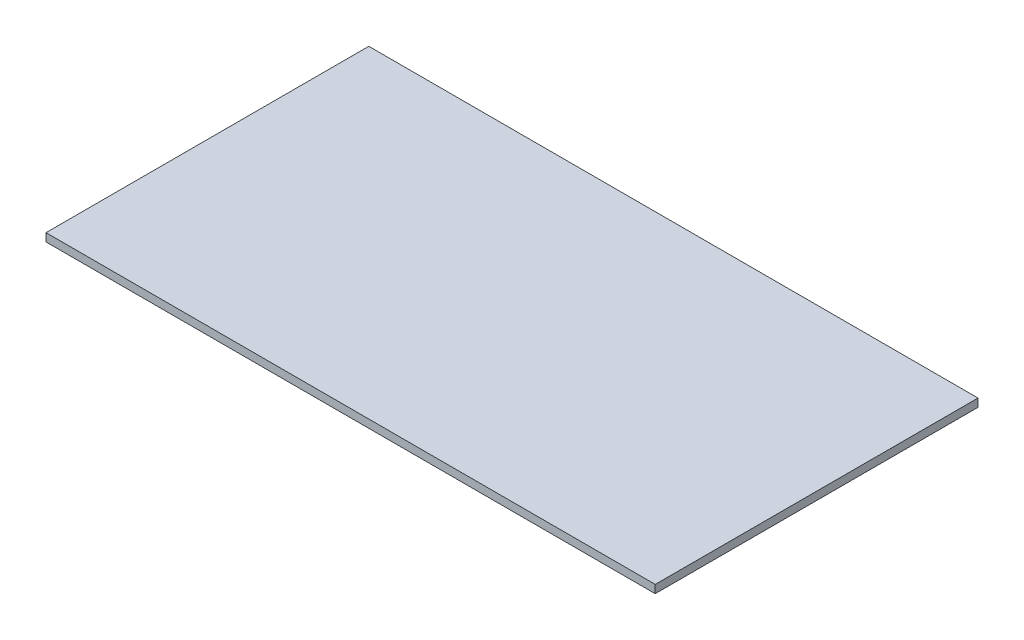
SolidWorks part; units mm, degrees
ref_plane "Front Plane" through (0, 0, 0) normal (0, 0, 1) x (1, 0, 0)
ref_plane "Top Plane" through (0, 0, 0) normal (0, 1, 0) x (1, 0, 0)
ref_plane "Right Plane" through (0, 0, 0) normal (1, 0, 0) x (0, 0, -1)
sketch "Sketch1" plane through (0, 0, 0) normal (0, 0, 1) x (1, 0, 0)
  line L1 (0, 0) -> (155, 0)
  line L2 (0, 0) -> (0, 110)
  line L3 (0, 110) -> (155, 110)
  line L4 (155, 0) -> (155, 110)
  dimension "D1" = 155
  dimension "D2" = 110
extrude "Boss-Extrude1" add sketch "Sketch1" along normal blind 80 contours L2 L1 L4 L3
sketch "Sketch2" plane through (0, 0, 80) normal (0, 0, 1) x (1, 0, 0)
  line L0 (0, 110) -> (2, 110) construction
  line L1 (0, 110) -> (155, 110) construction
  line L2 (0, 110) -> (0, 108) construction
  line L3 (0, 0) -> (0, 110) construction
  line L4 (155, 0) -> (155, 2) construction
  line L5 (155, 0) -> (155, 110) construction
  line L6 (155, 0) -> (153, 0) construction
  line L7 (0, 0) -> (155, 0) construction
  line L8 (0, 108) -> (2, 108) construction
  line L9 (2, 108) -> (2, 110) construction
  line L10 (155, 2) -> (153, 2) construction
  line L11 (153, 2) -> (153, 0) construction
  line L13 (153, 2) -> (2, 2)
  line L14 (153, 2) -> (153, 108)
  line L15 (153, 108) -> (2, 108)
  line L16 (2, 2) -> (2, 108)
  dimension "D1" = 2
  dimension "D2" = 2
  dimension "D3" = 2
  dimension "D4" = 2
extrude "Cut-Extrude1" cut sketch "Sketch2" against normal blind 78 contours L14 L13 L16 L15
sketch "Sketch3" plane through (0, 0, 2) normal (0, 0, 1) x (1, 0, 0)
  line L0 (2, 2) -> (6, 2) construction
  line L1 (153, 2) -> (2, 2) construction
  line L2 (153, 2) -> (149, 2) construction
  line L3 (2, 108) -> (6, 108) construction
  line L4 (153, 108) -> (2, 108) construction
  line L5 (2, 108) -> (2, 104.5) construction
  line L6 (2, 2) -> (2, 108) construction
  line L7 (149, 2) -> (149, 5.5) construction
  line L8 (2, 104.5) -> (6, 104.5) construction
  line L9 (6, 104.5) -> (6, 108) construction
  line L10 (6, 5.5) -> (10, 5.5) construction
  line L11 (6, 104.5) -> (149, 104.5)
  line L12 (6, 104.5) -> (6, 5.5)
  line L13 (6, 5.5) -> (149, 5.5)
  line L14 (149, 104.5) -> (149, 5.5)
  line L15 (10, 5.5) -> (10, 9.5) construction
  line L16 (149, 104.5) -> (145, 104.5) construction
  line L17 (145, 104.5) -> (145, 100.5) construction
  line L19 (10, 9.5) -> (145, 9.5)
  line L20 (10, 9.5) -> (10, 100.5)
  line L21 (10, 100.5) -> (145, 100.5)
  line L22 (145, 9.5) -> (145, 100.5)
  circle A0 centre (145, 100.5) radius 2.5
  circle A1 centre (145, 9.5) radius 2.5
  circle A2 centre (10, 9.5) radius 2.5
  circle A3 centre (10, 100.5) radius 2.5
  dimension "D10" = 5
  dimension "D11" = 5
  dimension "D12" = 5
  dimension "D13" = 5
  dimension "D1" = 4
  dimension "D2" = 3.5
  dimension "D3" = 4
  dimension "D4" = 4
  dimension "D5" = 3.5
  dimension "D6" = 4
  dimension "D7" = 4
  dimension "D8" = 4
  dimension "D9" = 4
extrude "Cut-Extrude2" cut sketch "Sketch3" against normal blind 2 contours A3 | A0 | A2 | A1
sketch "Sketch4" plane through (155, 0, 0) normal (1, 0, 0) x (0, 0, -1)
  line L1 (-53.75, 59.1) -> (-26.25, 59.1)
  line L3 (0, 55) -> (-80, 55) construction
  line L4 (0, 0) -> (0, 110) construction
  line L5 (-80, 0) -> (-80, 110) construction
  line L7 (-26.25, 105.9) -> (-26.25, 59.1)
  line L14 (-53.75, 105.9) -> (-26.25, 105.9)
  line L15 (-53.75, 105.9) -> (-53.75, 59.1)
  dimension "D1" = 46.8
  dimension "D2" = 27.5
sketch "Sketch7" plane through (0, 110, 0) normal (0, 1, 0) x (1, 0, 0)
  line L0 (0, -40) -> (155, -40) construction
  line L1 (0, -80) -> (0, 0) construction
  line L2 (155, -80) -> (155, 0) construction
  line L3 (77.5, 0) -> (77.5, -80) construction
  line L4 (0, 0) -> (155, 0) construction
  line L5 (0, -80) -> (155, -80) construction
  line L6 (110.52, -65.4) -> (95.28, -65.4) construction
  line L7 (44.48, -65.4) -> (110.52, -65.4)
  line L8 (44.48, -65.4) -> (44.48, -14.6)
  line L9 (44.48, -14.6) -> (110.52, -14.6)
  line L10 (110.52, -65.4) -> (110.52, -14.6)
  line L11 (44.48, -65.4) -> (110.52, -14.6) construction
  line L12 (44.48, -14.6) -> (110.52, -65.4) construction
  line L13 (95.28, -65.4) -> (95.28, -62.86) construction
  line L14 (110.52, -14.6) -> (95.28, -14.6) construction
  line L15 (44.48, -14.6) -> (44.48, -20.1445) construction
  line L16 (44.48, -65.4) -> (44.48, -47.62) construction
  line L17 (95.28, -14.6) -> (95.28, -17.14) construction
  line L18 (44.48, -65.4) -> (44.48, -19.68) construction
  circle A0 centre (44.48, -20.1445) radius 1.6
  circle A1 centre (95.28, -17.14) radius 1.6
  circle A2 centre (95.28, -62.86) radius 1.6
  circle A3 centre (44.48, -47.62) radius 1.6
  point P12 (77.5, -40)
  dimension "D9" = 3.2
  dimension "D10" = 3.2
  dimension "D11" = 3.2
  dimension "D12" = 3.2
  dimension "D1" = 66.04
  dimension "D2" = 50.8
  dimension "D3" = 15.24
  dimension "D4" = 2.54
  dimension "D5" = 15.24
  dimension "D6" = 2.54
  dimension "D7" = 17.78
  dimension "D8" = 45.72
extrude "Cut-Extrude7" cut sketch "Sketch7" against normal blind 2 contours A0 | A1 | A3 | A2
extrude "Cut-Extrude8" cut sketch "Sketch4" against normal blind 2
sketch "Sketch8" plane through (155, 0, 0) normal (1, 0, 0) x (0, 0, -1)
  line L0 (-80, 55) -> (0, 55) construction
  line L1 (-80, 0) -> (-80, 110) construction
  line L2 (0, 0) -> (0, 110) construction
  line L3 (0, 0) -> (-2, 0) construction
  line L4 (-80, 0) -> (0, 0) construction
  line L5 (-2, 0) -> (-2, 2) construction
  line L6 (-80, 0) -> (-78, 0) construction
  line L7 (-78, 0) -> (-78, 2) construction
  line L8 (-70, 2) -> (-70, 55)
  line L9 (-78, 2) -> (-74, 2)
  line L10 (-78, 2) -> (-78, 55)
  line L11 (-78, 55) -> (-74, 55)
  line L12 (-74, 2) -> (-74, 55)
  line L13 (-70, 2) -> (-66, 2)
  line L14 (-66, 2) -> (-66, 55)
  line L15 (-70, 55) -> (-66, 55)
  line L16 (-62, 2) -> (-62, 55)
  line L17 (-62, 2) -> (-58, 2)
  line L18 (-58, 2) -> (-58, 55)
  line L19 (-62, 55) -> (-58, 55)
  line L20 (-54, 2) -> (-54, 55)
  line L21 (-54, 2) -> (-50, 2)
  line L22 (-50, 2) -> (-50, 55)
  line L23 (-54, 55) -> (-50, 55)
  line L24 (-46, 2) -> (-46, 55)
  line L25 (-46, 2) -> (-42, 2)
  line L26 (-42, 2) -> (-42, 55)
  line L27 (-46, 55) -> (-42, 55)
  line L28 (-38, 2) -> (-38, 55)
  line L29 (-38, 2) -> (-34, 2)
  line L30 (-34, 2) -> (-34, 55)
  line L31 (-38, 55) -> (-34, 55)
  line L32 (-30, 2) -> (-30, 55)
  line L33 (-30, 2) -> (-26, 2)
  line L34 (-26, 2) -> (-26, 55)
  line L35 (-30, 55) -> (-26, 55)
  line L36 (-22, 2) -> (-22, 55)
  line L37 (-22, 2) -> (-18, 2)
  line L38 (-18, 2) -> (-18, 55)
  line L39 (-22, 55) -> (-18, 55)
  line L40 (-14, 2) -> (-14, 55)
  line L41 (-14, 2) -> (-10, 2)
  line L42 (-10, 2) -> (-10, 55)
  line L43 (-14, 55) -> (-10, 55)
  line L44 (-6, 2) -> (-6, 55)
  line L45 (-6, 2) -> (-2, 2)
  line L46 (-2, 2) -> (-2, 55)
  line L47 (-6, 55) -> (-2, 55)
  dimension "D1" = 2
  dimension "D2" = 2
  dimension "D3" = 2
  dimension "D4" = 2
  dimension "D5" = 4
extrude "Cut-Extrude9" cut sketch "Sketch8" against normal blind 2
sketch "Sketch9" plane through (0, 110, 0) normal (0, 1, 0) x (1, 0, 0)
  line L0 (0, -40) -> (155, -40) construction
  line L1 (0, -80) -> (0, 0) construction
  line L2 (155, -80) -> (155, 0) construction
  line L3 (155, -40) -> (120, -40) construction
  line L4 (120, -40) -> (120, -26) construction
  line L5 (120, -26) -> (113, -26) construction
  line L7 (113, -26) -> (127, -26)
  line L8 (113, -26) -> (113, -12)
  line L9 (113, -12) -> (127, -12)
  line L10 (127, -26) -> (127, -12)
  dimension "D1" = 35
  dimension "D2" = 14
  dimension "D3" = 7
  dimension "D4" = 14
  dimension "D5" = 14
extrude "Cut-Extrude10" cut sketch "Sketch9" against normal blind 2
sketch "Sketch10" plane through (0, 0, 0) normal (-1, 0, 0) x (0, 0, 1)
  line L0 (40, 110) -> (40, 0) construction
  line L1 (80, 110) -> (0, 110) construction
  line L2 (80, 0) -> (0, 0) construction
  line L3 (80, 55) -> (0, 55) construction
  line L4 (80, 0) -> (80, 110) construction
  line L5 (0, 0) -> (0, 110) construction
  line L6 (40, 55) -> (80, 55) construction
  line L7 (80, 55) -> (60, 55) construction
  line L8 (60, 55) -> (58, 55) construction
  line L9 (40, 95) -> (42.5, 95) construction
  line L10 (40, 15) -> (76, 15)
  line L11 (40, 15) -> (40, 95)
  line L12 (40, 95) -> (76, 95)
  line L13 (76, 15) -> (76, 95)
  line L14 (40, 15) -> (76, 95) construction
  line L15 (40, 95) -> (76, 15) construction
  line L16 (42.5, 95) -> (42.5, 92.5) construction
  line L17 (76, 15) -> (73.5, 15) construction
  line L18 (73.5, 15) -> (73.5, 17.5) construction
  line L19 (76, 15) -> (76, 19.4) construction
  line L20 (42.5, 92.5) -> (73.5, 92.5)
  line L21 (42.5, 92.5) -> (42.5, 17.5)
  line L22 (42.5, 17.5) -> (73.5, 17.5)
  line L23 (73.5, 92.5) -> (73.5, 17.5)
  line L24 (76, 19.4) -> (70.6, 19.4) construction
  line L25 (40, 95) -> (45.4, 95) construction
  line L26 (45.4, 95) -> (45.4, 90.6) construction
  line L28 (45.4, 90.6) -> (70.6, 90.6)
  line L29 (45.4, 90.6) -> (45.4, 19.4)
  line L30 (45.4, 19.4) -> (70.6, 19.4)
  line L31 (70.6, 90.6) -> (70.6, 19.4)
  circle A0 centre (73.5, 92.5) radius 1.25
  circle A1 centre (73.5, 17.5) radius 1.25
  circle A2 centre (42.5, 17.5) radius 1.25
  circle A3 centre (42.5, 92.5) radius 1.25
  dimension "D8" = 2.5
  dimension "D9" = 2.5
  dimension "D10" = 2.5
  dimension "D11" = 2.5
  dimension "D1" = 2
  dimension "D2" = 80
  dimension "D3" = 36
  dimension "D4" = 2.5
  dimension "D5" = 2.5
  dimension "D6" = 2.5
  dimension "D7" = 2.5
  dimension "D12" = 4.4
  dimension "D13" = 5.4
  dimension "D14" = 4.4
  dimension "D15" = 5.4
extrude "Cut-Extrude12" cut sketch "Sketch10" against normal blind 2 contours L31 L28 L29 L30 | A3 | A0 | A2 | A1
sketch "Sketch11" plane through (0, 0, 0) normal (-1, 0, 0) x (0, 0, 1)
  line L0 (40, 110) -> (40, 0) construction
  line L1 (80, 110) -> (0, 110) construction
  line L2 (80, 0) -> (0, 0) construction
  line L3 (20, 110) -> (20, 0) construction
  line L4 (0, 55) -> (0, 110) construction
  line L5 (0, 0) -> (0, 110) construction
  line L6 (40, 55) -> (0, 55) construction
  line L7 (0, 82.5) -> (40, 82.5) construction
  circle A0 centre (20, 55) radius 2.5
  circle A1 centre (20, 40) radius 2.5
  circle A2 centre (20, 25) radius 2.5
  circle A3 centre (20, 82.5) radius 4.5
  dimension "D1" = 5
  dimension "D3" = 9
  dimension "D2" = 3
extrude "Cut-Extrude13" cut sketch "Sketch11" against normal blind 2
sketch "Sketch12" plane through (0, 0, 80) normal (0, 0, 1) x (1, 0, 0)
  line L0 (2, 2) -> (2, 0) construction
  line L1 (0, 0) -> (155, 0) construction
  line L2 (153, 2) -> (153, 0) construction
  line L4 (153, 0) -> (155, 0)
  line L5 (153, 0) -> (153, 110)
  line L6 (153, 110) -> (155, 110)
  line L7 (155, 0) -> (155, 110)
  line L8 (2, 0) -> (0, 0)
  line L9 (2, 0) -> (2, 110)
  line L10 (2, 110) -> (0, 110)
  line L11 (0, 0) -> (0, 110)
  line L12 (153, 2) -> (2, 2)
  line L13 (153, 2) -> (153, 110)
  line L14 (153, 110) -> (2, 110)
  line L15 (2, 2) -> (2, 110)
  line M1 (2, 108) -> (153, 108)
  line M2 (153, 108) -> (153, 2)
  line M3 (153, 2) -> (2, 2)
  line M4 (2, 2) -> (2, 108)
  line M5 (155, 110) -> (0, 110)
extrude "Cut-Extrude14" cut sketch "Sketch12" against normal blind 80 contours M1 M4 M3 M2 | L9 L5 M1 M5
